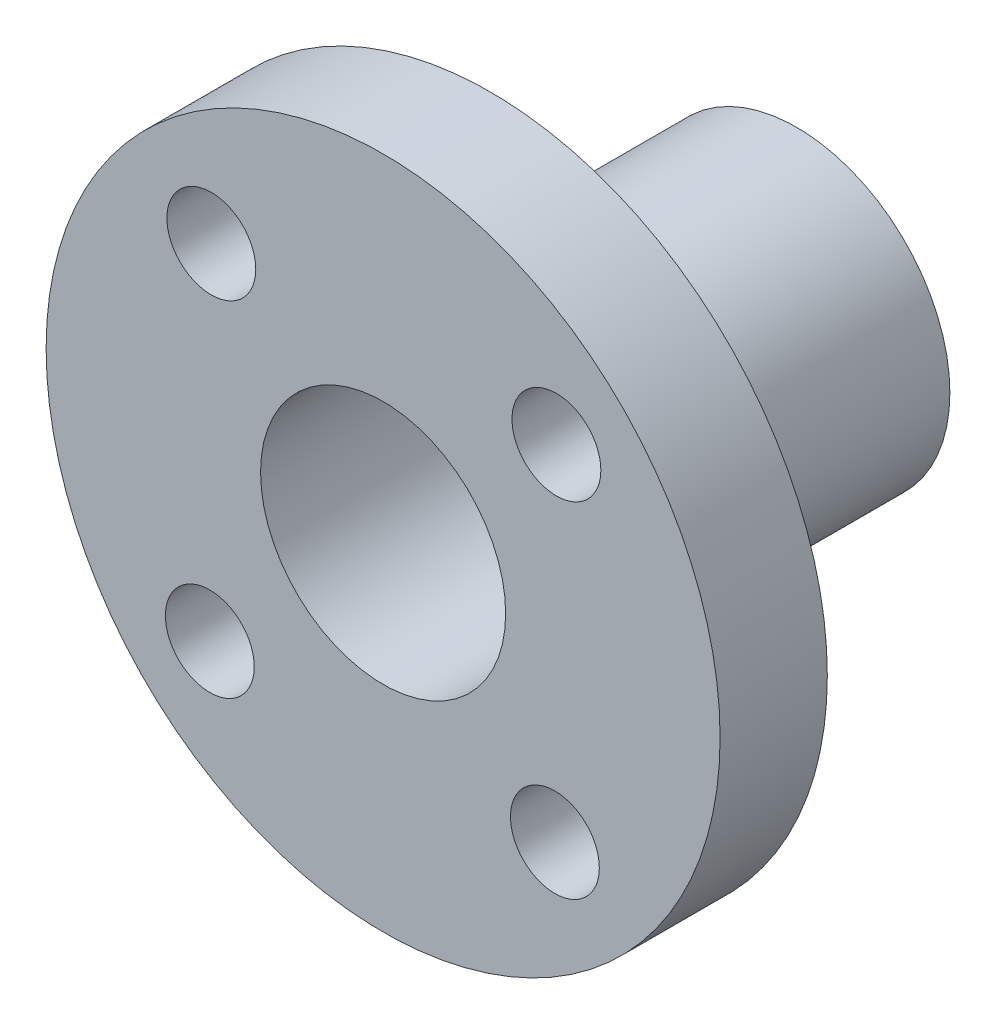
SolidWorks part; units mm, degrees
material "Fósforo-bronze  10% D, UNS C52400"
ref_plane "Front Plane" through (0, 0, 0) normal (0, 0, 1) x (1, 0, 0)
ref_plane "Top Plane" through (0, 0, 0) normal (0, 1, 0) x (1, 0, 0)
ref_plane "Right Plane" through (0, 0, 0) normal (1, 0, 0) x (0, 0, -1)
sketch "Sketch1" plane through (0, 0, 0) normal (0, 0, 1) x (1, 0, 0)
  circle A0 centre (0.05, 219.95) radius 11
  circle A1 centre (0.05, 219.95) radius 4
  circle A2 centre (5.6569, 214.2931) radius 1.45
  circle A3 centre (-5.6069, 214.3431) radius 1.45
  circle A4 centre (-5.5569, 225.6069) radius 1.45
  circle A5 centre (5.7069, 225.5569) radius 1.45
  point P16 (0.05, 219.95)
  dimension "D1" = 4
extrude "Boss-Extrude1" add sketch "Sketch1" along normal blind 3.5
sketch "Sketch2" plane through (0, 0, 0) normal (0, 0, -1) x (-1, 0, 0)
  circle A0 centre (-0.05, 219.95) radius 5
  circle A1 centre (-0.05, 219.95) radius 4
  dimension "D1" = 10
  dimension "D2" = 8
extrude "Boss-Extrude2" add sketch "Sketch2" along normal blind 10
